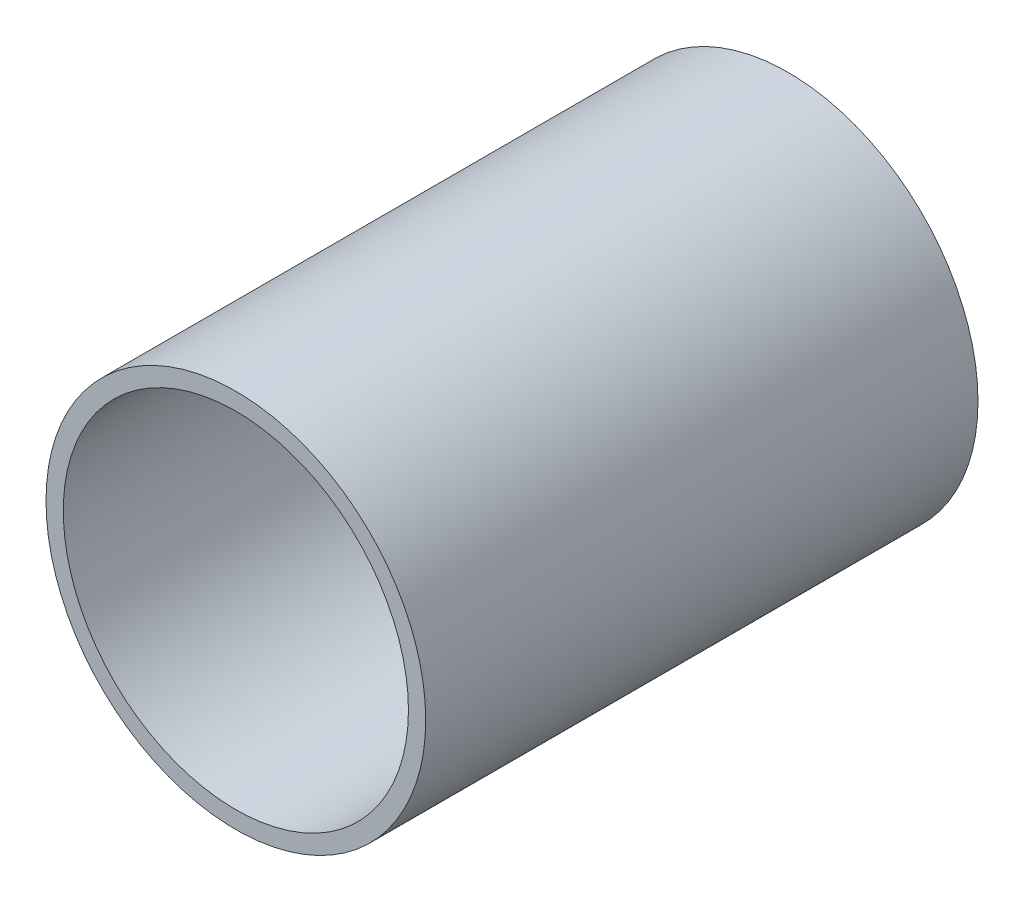
SolidWorks part; units mm, degrees
ref_plane "Plan1" through (0, 0, 0) normal (0, 0, 1) x (1, 0, 0)
ref_plane "Plan2" through (0, 0, 0) normal (0, 1, 0) x (1, 0, 0)
ref_plane "Plan3" through (0, 0, 0) normal (1, 0, 0) x (0, 0, -1)
sketch "Esquisse1" plane through (0, 0, 0) normal (0, 0, 1) x (1, 0, 0)
  circle A0 centre (0, 0) radius 12.5
  circle A1 centre (0, 0) radius 13.75
  dimension "D1" = 25
  dimension "D2" = 27.5
extrude "Base-Extrusion" add sketch "Esquisse1" along normal blind 40
